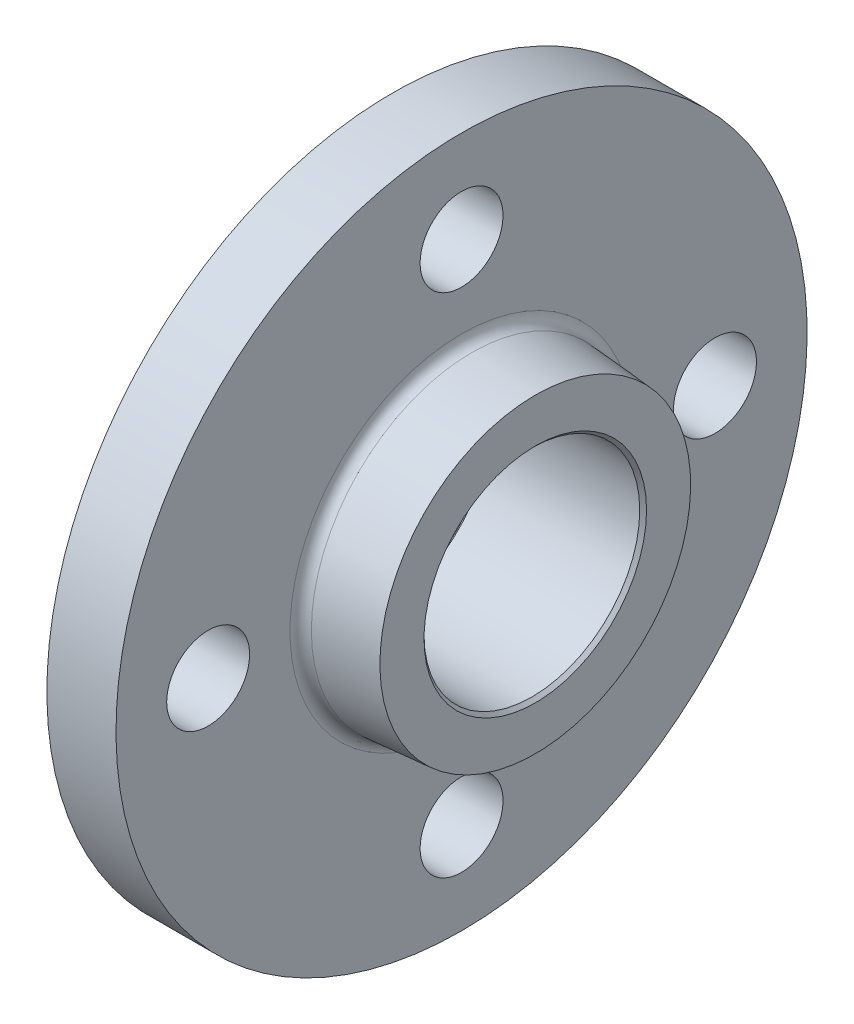
SolidWorks part; units mm, degrees
material "AISI 316 Stainless Steel Sheet (SS)"
ref_plane "Front Plane" through (0, 0, 0) normal (0, 0, 1) x (1, 0, 0)
ref_plane "Top Plane" through (0, 0, 0) normal (0, 1, 0) x (1, 0, 0)
ref_plane "Right Plane" through (0, 0, 0) normal (1, 0, 0) x (0, 0, -1)
ref_plane "Plane1" through (0, 0, 0) normal (0, 0, -1) x (-1, 0, 0)
sketch "Sketch1" plane through (0, 0, 0) normal (0, 0, -1) x (-1, 0, 0)
  line L0 (-18, 75) -> (-18, 0)
  line L1 (-18, 0) -> (-3, 0)
  line L2 (-3, 0) -> (-3, 75)
  line L3 (-3, 75) -> (-18, 75)
  line L4 (-18, 0) -> (-3, 0) construction
revolve "Revolve1" add sketch "Sketch1" angle 360 about L4
sketch "Sketch2" plane through (3, 0, 0) normal (-1, 0, 0) x (0, 0, 1)
  circle A0 centre (0, 0) radius 44
extrude "Boss-Extrude1" add sketch "Sketch2" along normal blind 3
sketch "Sketch3" plane through (18, 0, 0) normal (1, 0, 0) x (0, 0, -1)
  circle A0 centre (0, 0) radius 35
extrude "Boss-Extrude2" add sketch "Sketch3" along normal blind 16 draft 4.574
hole_wizard "Ø18.0 (18) Diameter Hole1" positions "Sketch5" profile "Sketch4" hole size "Ø18.0" standard "ANSI Metric"
sketch "Sketch5" plane through (3, 0, 0) normal (-1, 0, 0) x (0, 0, 1)
  point P0 (0, -55)
  point P1 (-55, 0)
  point P2 (0, 55)
  point P3 (55, 0)
sketch "Sketch4" plane through (3, -55, 0) normal (0, 1, 0) x (0, 0, 1)
  line L0 (0, 0) -> (0, 31)
  line L1 (0, 31) -> (9, 31)
  line L2 (9, 31) -> (9, 0)
  line L5 (9, 0) -> (0, 0)
  line L11 (0, -6.35) -> (0, 107.95) construction
  dimension "Thru Hole Dia." = 18
  dimension "Thru Hole Depth" = 31
hole_wizard "M42 Clearance Hole1" positions "Sketch7" profile "Sketch6" hole size "M42" standard "ANSI Metric"
sketch "Sketch7" plane through (34, 0, 0) normal (1, 0, 0) x (0, 0, -1)
  point P0 (0, 0)
sketch "Sketch6" plane through (34, 0, 0) normal (0, 1, 0) x (0, 0, -1)
  line L0 (0, 0) -> (0, 34)
  line L1 (0, 34) -> (23.4105, 34)
  line L2 (23.4105, 34) -> (23.4105, 0)
  line L5 (23.4105, 0) -> (0, 0)
  line L11 (0, -6.35) -> (0, 107.95) construction
  dimension "Thru Hole Dia." = 46.8209
  dimension "Thru Hole Depth" = 34
chamfer "Chamfer1" distance 0.7395 angle 45 2 edges at (0, 0, -23.4105) (34, 0, -23.4105)
fillet "Fillet1" radius 2.415 1 edges at (18, 35, 0)
